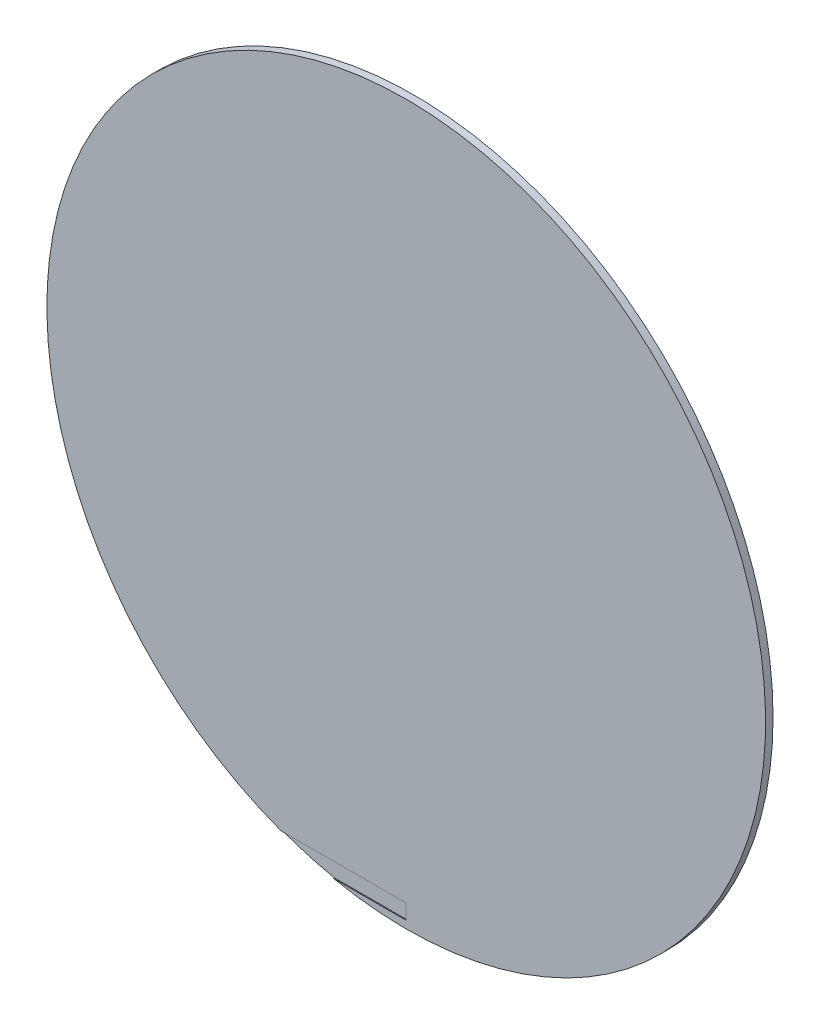
SolidWorks part; units mm, degrees
ref_plane "Front Plane" through (0, 0, 0) normal (0, 0, 1) x (1, 0, 0)
ref_plane "Top Plane" through (0, 0, 0) normal (0, 1, 0) x (1, 0, 0)
ref_plane "Right Plane" through (0, 0, 0) normal (1, 0, 0) x (0, 0, -1)
sketch "Sketch1" plane through (0, 0, 0) normal (0, 0, 1) x (1, 0, 0)
  circle A0 centre (0, 0) radius 152.4
  dimension "D1" = 304.8
extrude "Boss-Extrude1" add sketch "Sketch1" along normal blind 3.175
sketch "Sketch2" plane through (0, 0, 0) normal (0, 0, -1) x (-1, 0, 0)
  line L0 (0, 0) -> (0, -152.4) construction
  line L1 (0, -149.225) -> (0, -142.875)
  line L2 (0, -142.875) -> (117.6695, -142.875)
  line L3 (117.6695, -142.875) -> (117.6695, -149.225)
  line L4 (117.6695, -149.225) -> (0, -149.225)
  circle A0 centre (0, 0) radius 152.4 construction
  dimension "D1" = 6.35
  dimension "D2" = 149.225
  dimension "D3" = 117.6695
extrude "Cut-Extrude2" cut sketch "Sketch2" along normal blind 0.3969 from offset 3.175
